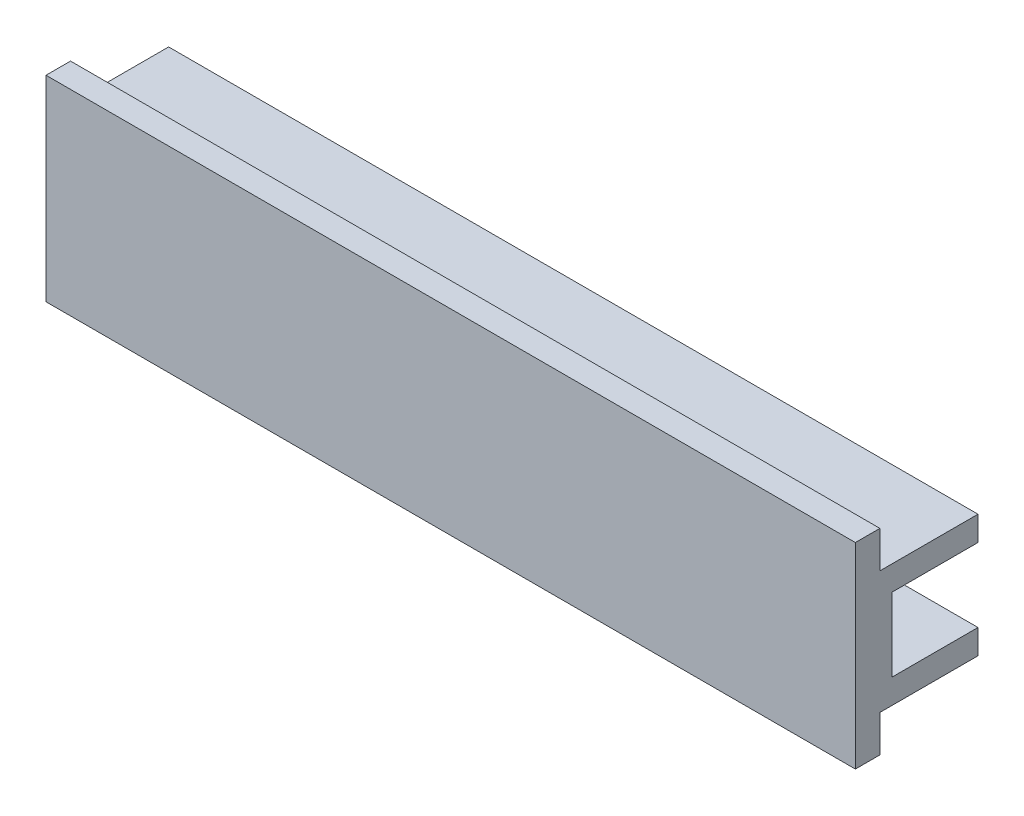
SolidWorks part; units mm, degrees
ref_plane "Front Plane" through (0, 0, 0) normal (0, 0, 1) x (1, 0, 0)
ref_plane "Top Plane" through (0, 0, 0) normal (0, 1, 0) x (1, 0, 0)
ref_plane "Right Plane" through (0, 0, 0) normal (1, 0, 0) x (0, 0, -1)
sketch "Sketch1" plane through (0, 0, 0) normal (1, 0, 0) x (0, 0, -1)
  line L0 (-3, 8) -> (-3, 5)
  line L1 (-5, 8) -> (-3, 8)
  line L2 (-5, 8) -> (-5, -8)
  line L3 (-5, -8) -> (-3, -8)
  line L4 (5, 5) -> (5, 3)
  line L5 (-5, 8) -> (5, -8) construction
  line L6 (-5, -8) -> (5, 8) construction
  line L7 (-3, 5) -> (5, 5)
  line L8 (5, 3) -> (-2, 3)
  line L9 (-2, 3) -> (-2, -3)
  line L10 (-2, -3) -> (5, -3)
  line L11 (5, -5) -> (-3, -5)
  line L12 (-3, -5) -> (-3, -8)
  line L13 (5, -3) -> (5, -5)
  point P0 (0, 0)
  dimension "D1" = 16
  dimension "D2" = 10
  dimension "D3" = 2
  dimension "D4" = 2
  dimension "D5" = 2
  dimension "D6" = 6
  dimension "D7" = 3
  dimension "D8" = 7
  dimension "D9" = 10
  dimension "D10" = 5
extrude "Extrude1" add sketch "Sketch1" along normal mid plane 66
sketch "Sketch2" plane through (-33, 0, 0) normal (-1, 0, 0) x (0, 0, 1)
  line L0 (2, 3) -> (3, 3)
  line L1 (3, 3) -> (3, -3)
  line L2 (3, -3) -> (2, -3)
  line L3 (2, -3) -> (2, 3)
  dimension "D1" = 1
extrude "Extrude2" cut sketch "Sketch2" against normal blind 56.5
sketch "Sketch3" plane through (0, 0, 2) normal (0, 0, -1) x (-1, 0, 0)
  line L0 (-23.5, 3) -> (-23.5, -3) construction
  line L1 (-23.5, 3) -> (-23.5, -3)
  arc A0 (-23.5, 3) -> (-23.5, -3) centre (-23.5, 0) ccw
extrude "Extrude3" cut sketch "Sketch3" against normal up to surface (1 mm away) up to face at (-4.75, 0, 3)
